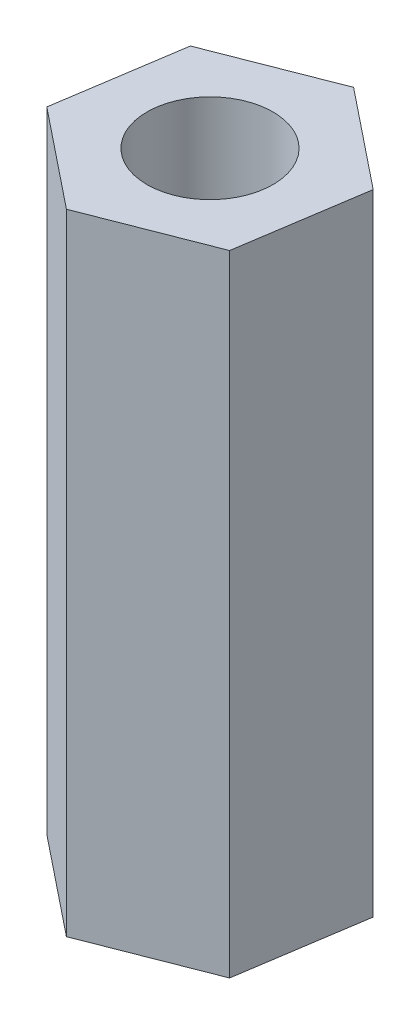
SolidWorks part; units mm, degrees
ref_plane "Front Plane" through (0, 0, 0) normal (0, 0, 1) x (1, 0, 0)
ref_plane "Top Plane" through (0, 0, 0) normal (0, 1, 0) x (1, 0, 0)
ref_plane "Right Plane" through (0, 0, 0) normal (1, 0, 0) x (0, 0, -1)
sketch "Sketch1" plane through (0, 0, 0) normal (0, 1, 0) x (1, 0, 0)
  line L1 (2.7947, 1.0906) -> (0.4529, 2.9656)
  line L2 (0.4529, 2.9656) -> (-2.3419, 1.875)
  line L3 (-2.3419, 1.875) -> (-2.7947, -1.0906)
  line L4 (-2.7947, -1.0906) -> (-0.4529, -2.9656)
  line L5 (-0.4529, -2.9656) -> (2.3419, -1.875)
  line L6 (2.3419, -1.875) -> (2.7947, 1.0906)
  circle A0 centre (0, 0) radius 2.5981 construction
  dimension "D1" = 3
extrude "Boss-Extrude1" add sketch "Sketch1" against normal blind 15
sketch "Sketch2" plane through (0, 0, 0) normal (0, 1, 0) x (1, 0, 0)
  circle A0 centre (0, 0) radius 1.5
extrude "Cut-Extrude1" cut sketch "Sketch2" against normal through all
